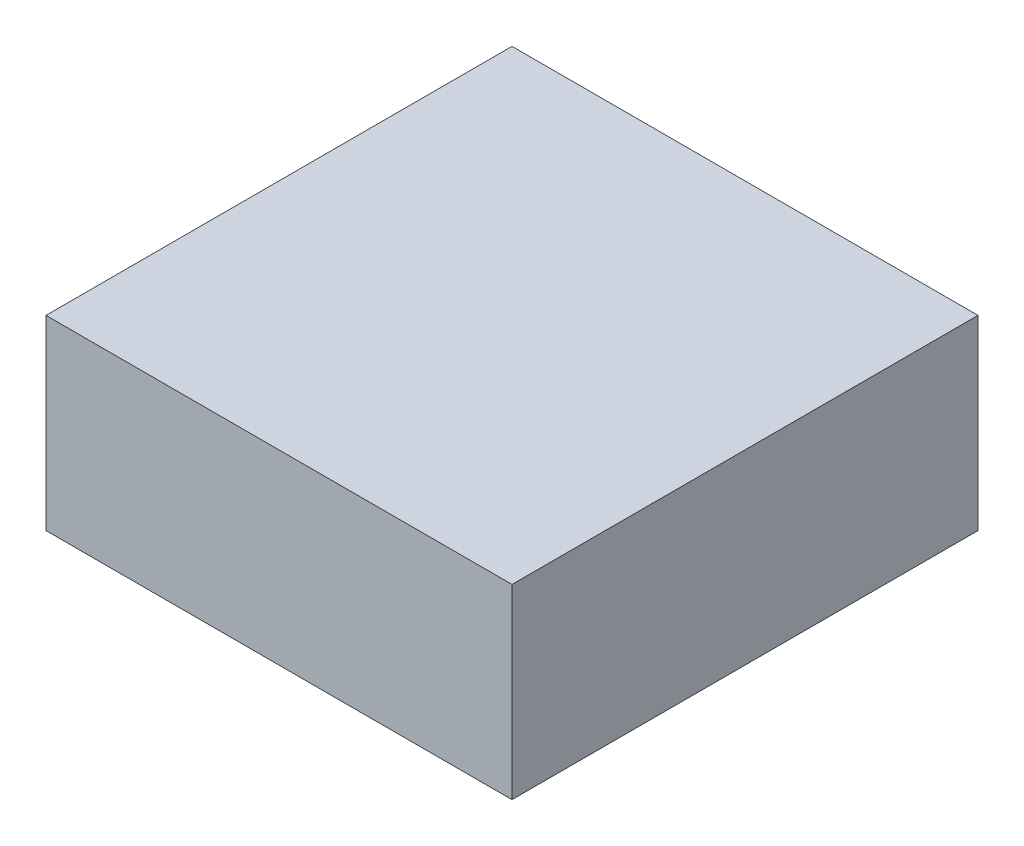
SolidWorks part; units mm, degrees
ref_plane "Front Plane" through (0, 0, 0) normal (0, 0, 1) x (1, 0, 0)
ref_plane "Top Plane" through (0, 0, 0) normal (0, 1, 0) x (1, 0, 0)
ref_plane "Right Plane" through (0, 0, 0) normal (1, 0, 0) x (0, 0, -1)
sketch "Sketch1" plane through (0, 0, 0) normal (0, 1, 0) x (1, 0, 0)
  line L1 (-0.5, 0.5) -> (0, 0.5)
  line L2 (-0.5, 0.5) -> (-0.5, 0)
  line L3 (-0.5, 0) -> (0, 0)
  line L4 (0, 0.5) -> (0, 0)
  dimension "D1" = 0.5
  dimension "D2" = 0.5
extrude "Boss-Extrude1" add sketch "Sketch1" along normal blind 0.2
